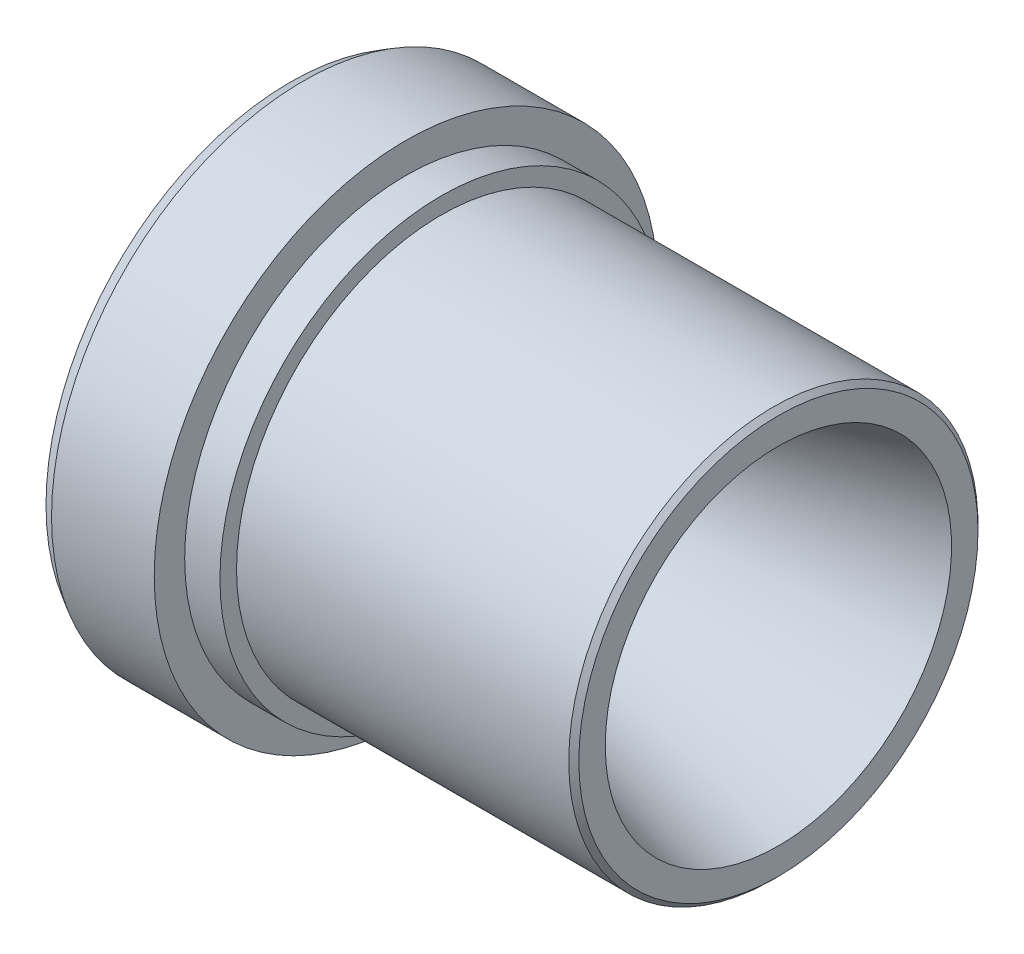
SolidWorks part; units mm, degrees
material "Glass Phenolic"
ref_plane "Front Plane" through (0, 0, 0) normal (0, 0, 1) x (1, 0, 0)
ref_plane "Top Plane" through (0, 0, 0) normal (0, 1, 0) x (1, 0, 0)
ref_plane "Right Plane" through (0, 0, 0) normal (1, 0, 0) x (0, 0, -1)
sketch "Sketch1" plane through (0, 0, 0) normal (0, 0, 1) x (1, 0, 0)
  line L0 (0, 7.9375) -> (0, 12.319)
  line L1 (0, 12.319) -> (0.6599, 12.7)
  line L2 (0.6599, 12.7) -> (5.842, 12.7)
  line L3 (5.842, 12.7) -> (5.842, 11.1633)
  line L4 (5.842, 11.1633) -> (7.62, 11.1633)
  line L5 (7.62, 11.1633) -> (7.62, 10.3251)
  line L6 (7.62, 10.3251) -> (24.384, 10.3251)
  line L7 (24.638, 10.0711) -> (24.638, 8.7376)
  line L8 (24.638, 8.7376) -> (5.842, 3.6957)
  line L9 (5.842, 3.6957) -> (4.2418, 3.6957)
  line L10 (4.2418, 3.6957) -> (0, 7.9375)
  line L11 (0, 0) -> (24.638, 0) construction
  line L12 (24.384, 10.3251) -> (24.638, 10.0711)
  point P3 (24.638, 10.3251)
  point P9 (0, 0)
  dimension "D1" = 5.842
  dimension "D2" = 7.62
  dimension "D3" = 0.762
  dimension "D4" = 30
  dimension "D5" = 12.7
  dimension "D6" = 7.9375
  dimension "D7" = 3.6957
  dimension "D8" = 1.6002
  dimension "D9" = 24.638
  dimension "D10" = 10.3251
  dimension "D11" = 8.7376
  dimension "D12" = 11.1633
  dimension "D13" = 0.254
  dimension "D14" = 45
revolve "Revolve1" add sketch "Sketch1" angle 360 about L11
